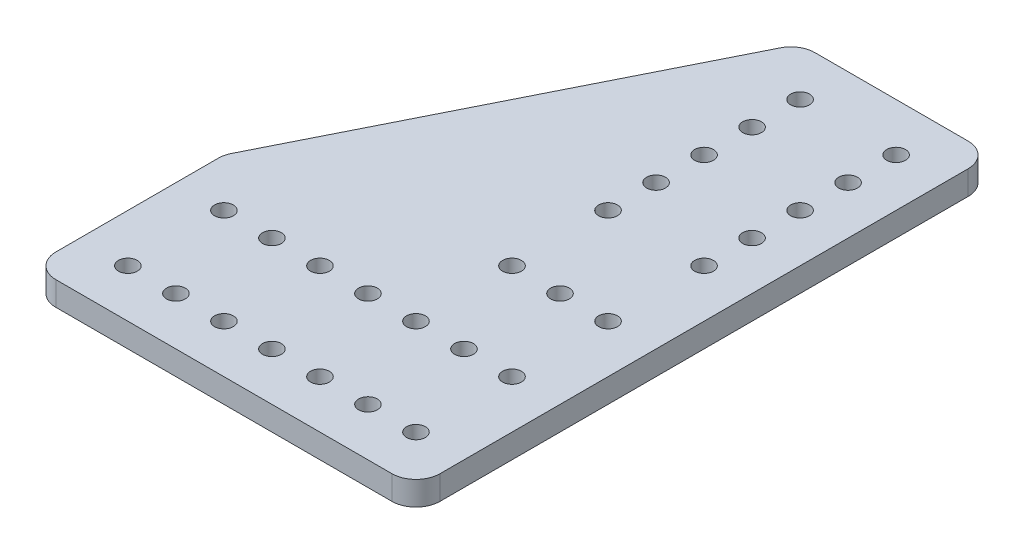
SolidWorks part; units mm, degrees
material "6061-T6 (SS)"
ref_plane "Front Plane" through (0, 0, 0) normal (0, 0, 1) x (1, 0, 0)
ref_plane "Top Plane" through (0, 0, 0) normal (0, 1, 0) x (1, 0, 0)
ref_plane "Right Plane" through (0, 0, 0) normal (1, 0, 0) x (0, 0, -1)
sketch "Sketch1" plane through (0, 0, 0) normal (0, 1, 0) x (1, 0, 0)
  line L0 (0, 50.8) -> (50.8, 152.4)
  line L1 (0, 0) -> (101.6, 0)
  line L2 (0, 0) -> (0, 50.8)
  line L3 (50.8, 152.4) -> (101.6, 152.4)
  line L4 (101.6, 0) -> (101.6, 152.4)
  dimension "D1" = 101.6
  dimension "D2" = 152.4
  dimension "D3" = 50.8
  dimension "D4" = 50.8
extrude "Boss-Extrude1" add sketch "Sketch1" along normal blind 6.35
sketch "Sketch2" plane through (0, 6.35, 0) normal (0, 1, 0) x (1, 0, 0)
  line L0 (0, 0) -> (101.6, 0) construction
  line L1 (101.6, 0) -> (101.6, 152.4) construction
  circle A0 centre (88.9, 12.7) radius 2.4892
  circle A1 centre (76.2, 12.7) radius 2.4892
  circle A2 centre (63.5, 12.7) radius 2.4892
  circle A3 centre (50.8, 12.7) radius 2.4892
  circle A4 centre (38.1, 12.7) radius 2.4892
  circle A5 centre (25.4, 12.7) radius 2.4892
  circle A6 centre (12.7, 12.7) radius 2.4892
  circle A7 centre (76.2, 25.4) radius 2.4892 construction
  circle A8 centre (63.5, 25.4) radius 2.4892 construction
  circle A9 centre (50.8, 25.4) radius 2.4892 construction
  circle A10 centre (38.1, 25.4) radius 2.4892 construction
  circle A11 centre (25.4, 25.4) radius 2.4892 construction
  circle A12 centre (12.7, 25.4) radius 2.4892 construction
  circle A13 centre (76.2, 38.1) radius 2.4892
  circle A14 centre (63.5, 38.1) radius 2.4892
  circle A15 centre (50.8, 38.1) radius 2.4892
  circle A16 centre (38.1, 38.1) radius 2.4892
  circle A17 centre (25.4, 38.1) radius 2.4892
  circle A18 centre (12.7, 38.1) radius 2.4892
  circle A19 centre (76.2, 50.8) radius 2.4892 construction
  circle A20 centre (63.5, 50.8) radius 2.4892 construction
  circle A21 centre (50.8, 50.8) radius 2.4892 construction
  circle A22 centre (38.1, 50.8) radius 2.4892 construction
  circle A23 centre (25.4, 50.8) radius 2.4892 construction
  circle A24 centre (12.7, 50.8) radius 2.4892 construction
  circle A25 centre (76.2, 63.5) radius 2.4892
  circle A26 centre (63.5, 63.5) radius 2.4892
  circle A27 centre (50.8, 63.5) radius 2.4892 construction
  circle A28 centre (38.1, 63.5) radius 2.4892 construction
  circle A29 centre (25.4, 63.5) radius 2.4892 construction
  circle A30 centre (12.7, 63.5) radius 2.4892 construction
  circle A31 centre (76.2, 76.2) radius 2.4892 construction
  circle A32 centre (63.5, 76.2) radius 2.4892 construction
  circle A33 centre (50.8, 76.2) radius 2.4892 construction
  circle A34 centre (38.1, 76.2) radius 2.4892 construction
  circle A35 centre (25.4, 76.2) radius 2.4892 construction
  circle A36 centre (12.7, 76.2) radius 2.4892 construction
  circle A37 centre (76.2, 88.9) radius 2.4892 construction
  circle A38 centre (63.5, 88.9) radius 2.4892
  circle A39 centre (50.8, 88.9) radius 2.4892 construction
  circle A40 centre (38.1, 88.9) radius 2.4892 construction
  circle A41 centre (25.4, 88.9) radius 2.4892 construction
  circle A42 centre (12.7, 88.9) radius 2.4892 construction
  circle A43 centre (76.2, 101.6) radius 2.4892 construction
  circle A44 centre (63.5, 101.6) radius 2.4892
  circle A45 centre (50.8, 101.6) radius 2.4892 construction
  circle A46 centre (38.1, 101.6) radius 2.4892 construction
  circle A47 centre (25.4, 101.6) radius 2.4892 construction
  circle A48 centre (12.7, 101.6) radius 2.4892 construction
  circle A49 centre (76.2, 114.3) radius 2.4892 construction
  circle A50 centre (63.5, 114.3) radius 2.4892
  circle A51 centre (50.8, 114.3) radius 2.4892 construction
  circle A52 centre (38.1, 114.3) radius 2.4892 construction
  circle A53 centre (25.4, 114.3) radius 2.4892 construction
  circle A54 centre (12.7, 114.3) radius 2.4892 construction
  circle A55 centre (76.2, 127) radius 2.4892 construction
  circle A56 centre (63.5, 127) radius 2.4892
  circle A57 centre (50.8, 127) radius 2.4892 construction
  circle A58 centre (38.1, 127) radius 2.4892 construction
  circle A59 centre (25.4, 127) radius 2.4892 construction
  circle A60 centre (12.7, 127) radius 2.4892 construction
  circle A61 centre (76.2, 139.7) radius 2.4892 construction
  circle A62 centre (63.5, 139.7) radius 2.4892
  circle A63 centre (50.8, 139.7) radius 2.4892 construction
  circle A64 centre (38.1, 139.7) radius 2.4892 construction
  circle A65 centre (25.4, 139.7) radius 2.4892 construction
  circle A66 centre (12.7, 139.7) radius 2.4892 construction
  circle A67 centre (88.9, 25.4) radius 2.4892 construction
  circle A68 centre (88.9, 38.1) radius 2.4892
  circle A69 centre (88.9, 50.8) radius 2.4892 construction
  circle A70 centre (88.9, 63.5) radius 2.4892
  circle A71 centre (88.9, 76.2) radius 2.4892 construction
  circle A72 centre (88.9, 88.9) radius 2.4892
  circle A73 centre (88.9, 101.6) radius 2.4892
  circle A74 centre (88.9, 114.3) radius 2.4892
  circle A75 centre (88.9, 127) radius 2.4892
  circle A76 centre (88.9, 139.7) radius 2.4892
  dimension "D2" = 12.7
  dimension "D3" = 4.9784
  dimension "D6" = 12.7
  dimension "D7" = 12.7
  dimension "D1" = 12.7
  dimension "D5" = 7
  dimension "D4" = 11
extrude "Cut-Extrude1" cut sketch "Sketch2" against normal through all
fillet "Fillet1" radius 6.35 5 edges at (0, 3.175, -50.8) (101.6, 3.175, -152.4) (101.6, 3.175, 0) (0, 3.175, 0) (50.8, 3.175, -152.4)
